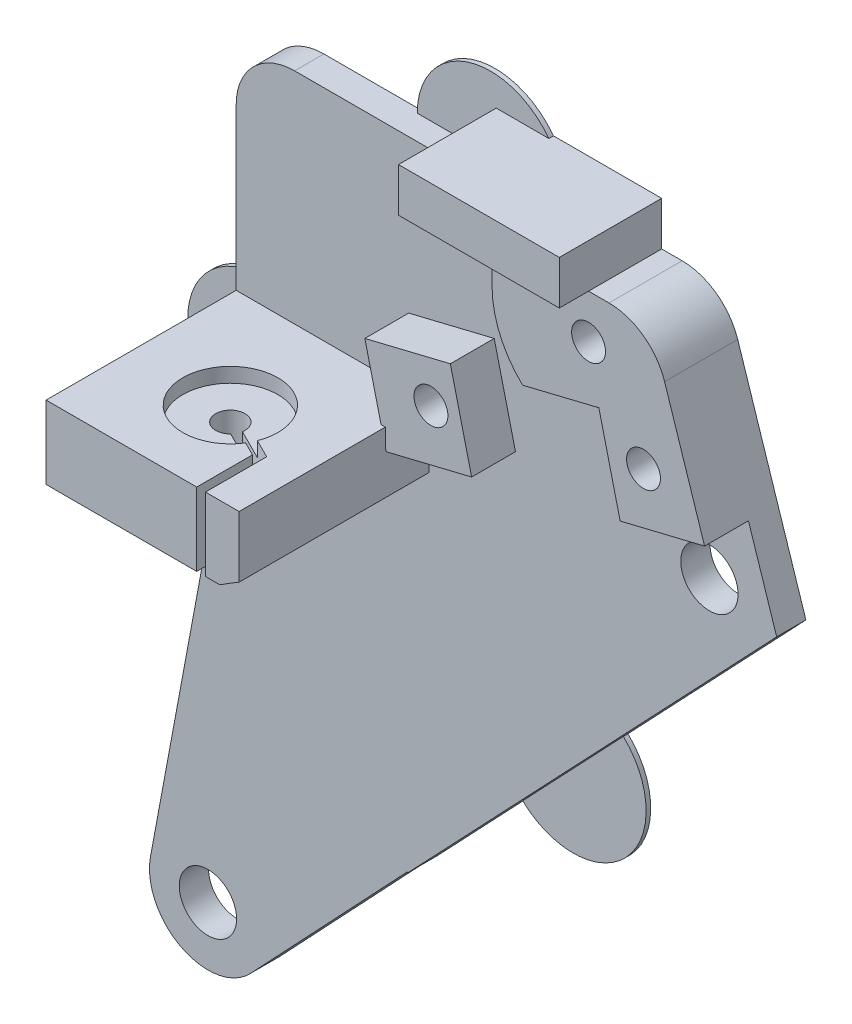
SolidWorks part; units mm, degrees
ref_plane "Front Plane" through (0, 0, 0) normal (0, 0, 1) x (1, 0, 0)
ref_plane "Top Plane" through (0, 0, 0) normal (0, 1, 0) x (1, 0, 0)
ref_plane "Right Plane" through (0, 0, 0) normal (1, 0, 0) x (0, 0, -1)
sketch "Sketch1" plane through (0, 0, 0) normal (0, 0, 1) x (1, 0, 0)
  line L12 (-28.2, 23.755) -> (-28.2, -23.755)
  line L13 (-23.755, -28.2) -> (23.755, -28.2)
  line L14 (28.2, -23.755) -> (28.2, 23.755)
  line L15 (23.755, 28.2) -> (-23.755, 28.2)
  circle A0 centre (0, 0) radius 19.05
  circle A1 centre (-23.57, 23.57) radius 2.55
  circle A2 centre (23.57, 23.57) radius 2.55
  circle A3 centre (23.57, -23.57) radius 2.55
  circle A4 centre (-23.57, -23.57) radius 2.55
  arc A12 (-23.755, 28.2) -> (-28.2, 23.755) centre (-23.755, 23.755) ccw
  arc A13 (-28.2, -23.755) -> (-23.755, -28.2) centre (-23.755, -23.755) ccw
  arc A14 (23.755, -28.2) -> (28.2, -23.755) centre (23.755, -23.755) ccw
  arc A15 (28.2, 23.755) -> (23.755, 28.2) centre (23.755, 23.755) ccw
sketch "Sketch2" plane through (0, 0, 0) normal (0, 0, 1) x (1, 0, 0)
  line L0 (-33.02, 0) -> (-33.02, 66.04) construction
  line L1 (-17.0688, -8.4592) -> (-41.402, 40.64)
  line L2 (-41.402, 66.04) -> (-1.524, 66.04)
  line L3 (-1.524, 66.04) -> (18.1091, 5.9131)
  line L4 (-41.402, 40.64) -> (-41.402, 66.04)
  arc A0 (-17.0688, -8.4592) -> (18.1091, 5.9131) centre (0, 0) ccw
  circle A1 centre (0, 0) radius 33.02 construction
  circle A2 centre (0, 0) radius 38.1 construction
  circle A3 centre (0, 0) radius 3.81
  dimension "D1" = 38.1
  dimension "D2" = 66.04
  dimension "D3" = 66.04
  dimension "D5" = 76.2
  dimension "D8" = 7.62
  dimension "D4" = 39.878
  dimension "D6" = 8.382
  dimension "D7" = 25.4
extrude "Boss-Extrude1" add sketch "Sketch2" along normal blind 2.54
sketch "Sketch5" plane through (0, 0, 2.54) normal (0, 0, 1) x (1, 0, 0)
  line L0 (-33.02, 0) -> (-33.02, 66.04) construction
  line L1 (-24.638, 40.64) -> (-41.402, 40.64)
  line L2 (-24.638, 40.64) -> (-24.638, 46.99)
  line L3 (-24.638, 46.99) -> (-41.402, 46.99)
  line L4 (-41.402, 40.64) -> (-41.402, 46.99)
  line L5 (-24.638, 40.64) -> (-41.402, 46.99) construction
  line L6 (-24.638, 46.99) -> (-41.402, 40.64) construction
  point P0 (-33.02, 43.815)
  dimension "D1" = 6.35
extrude "Boss-Extrude2" add sketch "Sketch5" along normal blind 16.51
sketch "Sketch6" plane through (0, 46.99, 0) normal (0, 1, 0) x (1, 0, 0)
  line L0 (-33.02, -2.54) -> (-33.02, -19.05) construction
  line L1 (-24.638, -2.54) -> (-41.402, -2.54) construction
  line L2 (-24.638, -19.05) -> (-41.402, -19.05) construction
  line L3 (-1.524, -2.54) -> (-41.402, -2.54) construction
  circle A0 centre (-33.02, -11.43) radius 4.1275
  dimension "D1" = 8.255
  dimension "0.4" = 8.89
extrude "Cut-Extrude2" cut sketch "Sketch6" against normal blind 1.27
sketch "Sketch7" plane through (0, 45.72, 0) normal (0, 1, 0) x (1, 0, 0)
  circle A0 centre (-33.02, -11.43) radius 1.27
  dimension "D1" = 2.54
extrude "Cut-Extrude3" cut sketch "Sketch7" against normal through all
sketch "Sketch9" plane through (0, 0, 0) normal (0, 0, -1) x (-1, 0, 0)
  line L0 (6.9839, 62.23) -> (3.1711, 62.23) construction
  line L1 (3.1711, 62.23) -> (5.0775, 58.928)
  line L2 (5.0775, 58.928) -> (8.8904, 58.928)
  line L3 (8.8904, 58.928) -> (10.7968, 62.23)
  line L4 (10.7968, 62.23) -> (8.8904, 65.532)
  line L5 (8.8904, 65.532) -> (5.0775, 65.532)
  line L6 (5.0775, 65.532) -> (3.1711, 62.23)
  line L7 (6.9839, 60.5028) -> (6.9839, 63.9572) construction
  line L8 (24.3799, 49.664) -> (23.3081, 53.3231)
  line L9 (23.3081, 53.3231) -> (19.6034, 54.2245)
  line L10 (19.6034, 54.2245) -> (16.9704, 51.4668)
  line L11 (16.9704, 51.4668) -> (18.0421, 47.8077)
  line L12 (18.0421, 47.8077) -> (21.7469, 46.9063)
  line L13 (21.7469, 46.9063) -> (24.3799, 49.664)
  line L14 (5.9185, 54.1558) -> (4.8467, 57.8149)
  line L15 (4.8467, 57.8149) -> (1.142, 58.7163)
  line L16 (1.142, 58.7163) -> (-1.491, 55.9586)
  line L17 (-1.491, 55.9586) -> (-0.4193, 52.2995)
  line L18 (-0.4193, 52.2995) -> (3.2855, 51.3981)
  line L19 (3.2855, 51.3981) -> (5.9185, 54.1558)
  line L21 (24.9034, 50.8527) -> (-13.9627, 60.3092) construction
  circle A0 centre (6.9839, 62.23) radius 3.302 construction
  circle A1 centre (20.6751, 50.5654) radius 3.302 construction
  circle A2 centre (2.2137, 55.0572) radius 3.302 construction
  circle A3 centre (6.9839, 62.23) radius 1.7272 construction
  circle A4 centre (2.2137, 55.0572) radius 1.5 construction
  circle A5 centre (20.6751, 50.5654) radius 1.5 construction
  dimension "D1" = 6.604
  dimension "D2" = 6.604
  dimension "D3" = 6.604
extrude "Cut-Extrude4" cut sketch "Sketch9" against normal blind 2.286
sketch "Sketch8" plane through (0, 0, 2.54) normal (0, 0, 1) x (1, 0, 0)
  line L0 (-41.402, 66.04) -> (-1.524, 66.04) construction
  line L1 (-15.367, 66.04) -> (-6.9839, 66.04)
  line L2 (-15.367, 66.04) -> (-15.367, 62.23)
  line L3 (-14.4512, 58.42) -> (-6.9839, 58.42) construction
  line L4 (-6.9839, 66.04) -> (-6.9839, 58.42) construction
  line L5 (-15.875, 63.5) -> (-15.875, 55.88) construction
  line L6 (-18.9903, 54.5774) -> (0.6579, 59.358) construction
  line L8 (-15.367, 62.23) -> (-6.9839, 62.23) construction
  line L9 (-6.9839, 66.04) -> (-1.524, 66.04)
  line L10 (-1.524, 66.04) -> (3.0918, 51.9041)
  line L11 (18.1091, 5.9131) -> (-1.524, 66.04) construction
  line L12 (-5.8104, 55.4982) -> (-4.2737, 49.1825) construction
  line L13 (-1.524, 66.04) -> (18.1091, 5.9131) construction
  line L14 (-4.2737, 49.1825) -> (-16.6817, 46.1635) construction
  line L15 (-16.6817, 46.1635) -> (-18.7435, 54.6374) construction
  line L16 (-6.0887, 57.7165) -> (-4.2404, 50.1201)
  line L17 (-17.142, 46.981) -> (-18.9903, 54.5774)
  line L18 (3.0918, 51.9041) -> (-4.2404, 50.1201)
  line L19 (-24.9034, 53.1387) -> (13.9627, 62.5952) construction
  line L20 (-5.5636, 55.5583) -> (-4.0269, 49.2425) construction
  line L21 (-12.7085, 56.1058) -> (-6.0887, 57.7165)
  line L22 (-16.9285, 46.1034) -> (-18.9903, 54.5774) construction
  line L23 (-17.142, 46.981) -> (-24.5674, 45.1744)
  line L24 (-24.5674, 45.1744) -> (-26.4157, 52.7707)
  line L25 (-26.4157, 52.7707) -> (-18.9903, 54.5774)
  line L26 (-21.1208, 35.3063) -> (-24.9034, 50.8527) construction
  line L27 (0.4193, 52.2995) -> (-3.2855, 51.3981) construction
  arc A0 (-6.9839, 58.42) -> (-6.9839, 66.04) centre (-6.9839, 62.23) ccw construction
  circle A1 centre (-20.6751, 50.5654) radius 3.4925 construction
  circle A2 centre (-2.2137, 55.0572) radius 3.4925 construction
  arc A3 (-15.367, 62.23) -> (-12.7085, 56.1058) centre (-6.9839, 62.23) ccw
  point P29 (-6.9839, 62.23)
  point P50 (-20.6751, 50.5654)
  point P52 (-2.2137, 55.0572)
  dimension "D2" = 6.985
  dimension "D3" = 6.985
  dimension "D1" = 0.508
  dimension "D4" = 0.254
  dimension "D5" = 1.016
  dimension "D6" = 1.016
extrude "Boss-Extrude3" add sketch "Sketch8" along normal blind 3.81
hole_wizard "#4 Clearance Hole1" positions "Sketch11" profile "Sketch10" hole size "#4" standard "ANSI Inch" end condition through all
sketch "Sketch11" plane through (0, 0, 6.35) normal (0, 0, 1) x (1, 0, 0)
  point P0 (-6.9839, 62.23)
  point P4 (-20.6751, 50.5654)
  point P7 (-2.2137, 55.0572)
sketch "Sketch10" plane through (-6.9839, 62.23, 6.35) normal (1, 0, 0) x (0, -1, 0)
  line L0 (0, 0) -> (0, 6.35)
  line L1 (0, 6.35) -> (1.4732, 6.35)
  line L2 (1.4732, 6.35) -> (1.4732, 0)
  line L5 (1.4732, 0) -> (0, 0)
  line L11 (0, -6.35) -> (0, 107.95) construction
  dimension "Thru Hole Dia." = 2.9464
  dimension "Thru Hole Depth" = 6.35
sketch "Sketch14" plane through (0, 0, 2.54) normal (0, 0, 1) x (1, 0, 0)
  line L1 (-41.402, 66.04) -> (-1.524, 66.04) construction
  line L2 (-6.9839, 60.7568) -> (-6.9839, 66.04) construction
  line L3 (-6.9839, 66.04) -> (-20.9539, 66.04)
  line L6 (-6.9839, 66.04) -> (-6.9839, 69.85)
  line L8 (-6.9839, 69.85) -> (-20.9539, 69.85)
  line L9 (-20.9539, 66.04) -> (-20.9539, 69.85)
  circle A0 centre (-6.9839, 62.23) radius 1.4732 construction
  point P0 (-6.9839, 62.23)
  dimension "D1" = 3.81
  dimension "D2" = 13.97
extrude "Boss-Extrude6" add sketch "Sketch14" along normal blind 6.35 and the other way through all
fillet "Fillet1" radius 5.08 2 edges at (-1.524, 66.04, 3.175) (-41.402, 66.04, 1.27)
sketch "Sketch15" plane through (0, 0, 2.54) normal (0, 0, 1) x (1, 0, 0)
  line L0 (-17.0688, -8.4592) -> (-41.402, 40.64) construction
  line L1 (-1.524, 66.04) -> (18.1091, 5.9131) construction
  arc A0 (-31.9429, 32.9938) -> (-0.299, 45.9222) centre (0, 0) cw construction
  circle A1 centre (0, 0) radius 3.81 construction
  arc A2 (-0.3152, 48.4114) -> (-33.6744, 34.7821) centre (0, 0) ccw
  arc A3 (-0.2828, 43.4331) -> (-30.2115, 31.2054) centre (0, 0) ccw
  arc A4 (-0.2828, 43.4331) -> (-0.3152, 48.4114) centre (-0.299, 45.9222) ccw
  arc A5 (-33.6744, 34.7821) -> (-30.2115, 31.2054) centre (-31.9429, 32.9938) ccw
  point P6 (-17.3687, 42.512)
  dimension "D1" = 4.9784
  dimension "D4" = 45.9232
  dimension "D2" = 5.08
  dimension "D3" = 5.08
extrude "Cut-Extrude5" cut sketch "Sketch15" against normal through all both and the other way through all
sketch "Sketch19" plane through (0, 0, 2.54) normal (0, 0, 1) x (1, 0, 0)
  line L0 (-0.299, 45.9222) -> (0, 0) construction
  line L1 (0, 0) -> (-48.9345, -0.3186) construction
  line L2 (-0.299, 45.9222) -> (-43.8546, -0.2855) construction
  line L3 (5.4662, 44.6323) -> (-40.158, -3.77)
  line L4 (3.3977, 42.4378) -> (-40.158, -3.77) construction
  line L5 (-1.524, 66.04) -> (18.1091, 5.9131) construction
  line L6 (-48.8488, 0.6444) -> (-41.402, 40.64)
  line L7 (-17.0688, -8.4592) -> (-41.402, 40.64) construction
  line L8 (-41.402, 40.64) -> (-26.3088, 40.64) construction
  line L9 (5.4662, 44.6323) -> (3.0918, 51.9041)
  line L10 (-4.2404, 50.1201) -> (3.0918, 51.9041) construction
  line L11 (3.0918, 51.9041) -> (-41.402, 40.64)
  circle A0 centre (-0.299, 45.9222) radius 2.4892
  circle A1 centre (-43.8546, -0.2855) radius 2.4892
  arc A2 (-48.8488, 0.6444) -> (-40.158, -3.77) centre (-43.8546, -0.2855) ccw
  dimension "D4" = 4.9784
  dimension "D5" = 5.08
  dimension "D1" = 90
  dimension "D2" = 45.9222
  dimension "D3" = 63.5
extrude "Boss-Extrude8" add sketch "Sketch19" against normal through all contours L6 L11 L9 L3 A2
sketch "Sketch20" plane through (0, 0, 2.54) normal (0, 0, 1) x (1, 0, 0)
  line L0 (-40.158, -3.77) -> (10.7295, 49.8638)
  line L1 (-40.158, -3.77) -> (-26.5483, 10.6684) construction
  line L2 (10.7295, 49.8638) -> (48.0717, 14.4336)
  line L3 (48.0717, 14.4336) -> (-7.6731, -44.3196)
  line L4 (-7.6731, -44.3196) -> (-40.158, -3.77)
  arc A0 (-48.8488, 0.6444) -> (-40.158, -3.77) centre (-43.8546, -0.2855) ccw construction
extrude "Cut-Extrude8" cut sketch "Sketch20" against normal blind 2.54
sketch "Sketch21" plane through (0, 46.99, 0) normal (0, 1, 0) x (1, 0, 0)
  line L0 (-27.94, -19.05) -> (-27.94, -13.97) construction
  line L1 (-24.638, -19.05) -> (-41.402, -19.05) construction
  line L2 (-27.94, -13.97) -> (-33.02, -11.43) construction
  line L3 (-27.559, -19.05) -> (-27.559, -13.7345)
  line L4 (-27.559, -13.7345) -> (-32.8496, -11.0892)
  line L5 (-28.321, -19.05) -> (-28.321, -14.2055)
  line L6 (-28.321, -14.2055) -> (-33.1904, -11.7708)
  line L7 (-33.1904, -11.7708) -> (-32.8496, -11.0892)
  line L8 (-28.321, -19.05) -> (-27.559, -19.05)
  dimension "D1" = 5.08
  dimension "D2" = 5.08
  dimension "D3" = 0.381
  dimension "D4" = 0.381
extrude "Cut-Extrude9" cut sketch "Sketch21" against normal through all contours L5 L6 L7 L4 L3 L8
sketch "Sketch13" plane through (0, 0, 0) normal (0, 0, -1) x (-1, 0, 0)
  line L0 (-5.5429, 44.3973) -> (26.5176, 10.6065) construction
  line L1 (41.402, 66.04) -> (1.524, 66.04) construction
  circle A0 centre (14.2843, 23.5001) radius 6.35
  circle A1 centre (21.463, 66.04) radius 6.35
  circle A2 centre (41.402, 40.64) radius 6.35
  dimension "D1" = 12.7
  dimension "D2" = 12.7
  dimension "D3" = 12.7
extrude "Print Tabs" add sketch "Sketch13" against normal blind 0.4
mirror "Mirror1" [suppressed] about plane through (0, 0, 0) normal (1, 0, 0)
